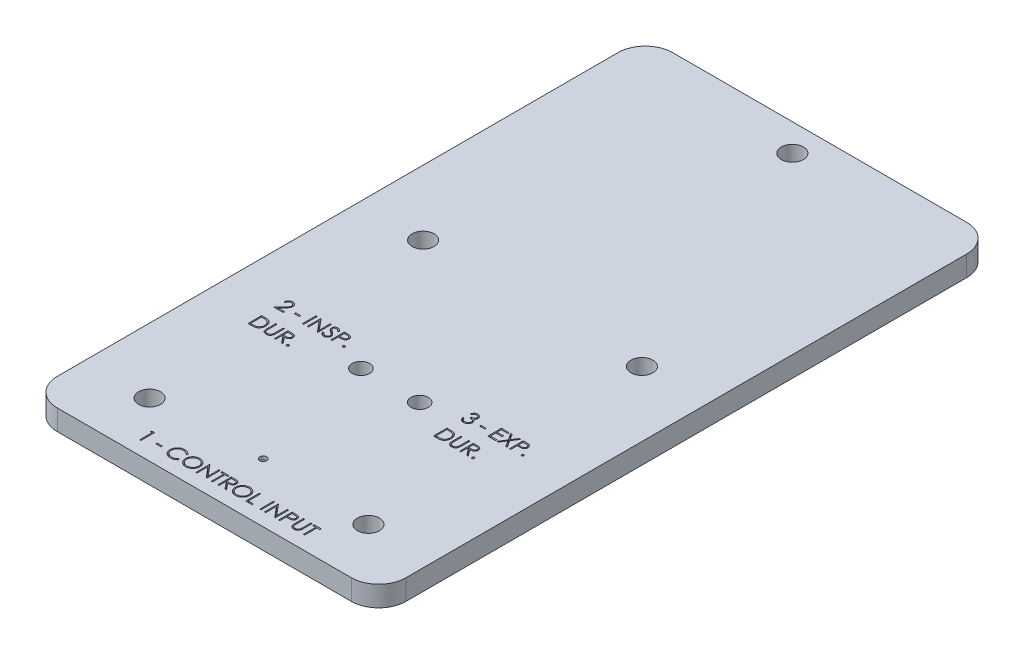
SolidWorks part; units mm, degrees
material "ABS"
ref_plane "Front Plane" through (0, 0, 0) normal (0, 0, 1) x (1, 0, 0)
ref_plane "Top Plane" through (0, 0, 0) normal (0, 1, 0) x (1, 0, 0)
ref_plane "Right Plane" through (0, 0, 0) normal (1, 0, 0) x (0, 0, -1)
sketch "Sketch2" plane through (0, 0, 0) normal (0, 1, 0) x (1, 0, 0)
  line L4 (-40.4812, 114.2369) -> (-40.4812, -15.9381)
  line L5 (-34.1312, -22.2881) -> (34.1313, -22.2881)
  line L6 (40.4813, -15.9381) -> (40.4813, 114.2369)
  line L7 (34.1313, 120.5869) -> (-34.1312, 120.5869)
  line L8 (-40.4812, 114.2369) -> (-40.4812, -15.9381)
  line L9 (-34.1312, -22.2881) -> (34.1313, -22.2881)
  line L10 (40.4813, -15.9381) -> (40.4813, 114.2369)
  line L11 (34.1313, 120.5869) -> (-34.1312, 120.5869)
  circle A0 centre (-25.4, -9.5881) radius 2.5527 construction
  circle A1 centre (25.4, -9.5881) radius 2.5527 construction
  circle A2 centre (25.4, 53.9119) radius 2.5527 construction
  circle A3 centre (0, 114.2369) radius 2.5527 construction
  arc A4 (-40.4812, -15.9381) -> (-34.1312, -22.2881) centre (-34.1312, -15.9381) ccw
  arc A5 (34.1313, -22.2881) -> (40.4813, -15.9381) centre (34.1313, -15.9381) ccw
  arc A6 (40.4813, 114.2369) -> (34.1313, 120.5869) centre (34.1313, 114.2369) ccw
  arc A7 (-34.1312, 120.5869) -> (-40.4812, 114.2369) centre (-34.1312, 114.2369) ccw
  arc A8 (-40.4812, -15.9381) -> (-34.1312, -22.2881) centre (-34.1312, -15.9381) ccw
  arc A9 (34.1313, -22.2881) -> (40.4813, -15.9381) centre (34.1313, -15.9381) ccw
  arc A10 (40.4813, 114.2369) -> (34.1313, 120.5869) centre (34.1313, 114.2369) ccw
  arc A11 (-34.1312, 120.5869) -> (-40.4812, 114.2369) centre (-34.1312, 114.2369) ccw
  circle A12 centre (-25.4, 53.9119) radius 2.5527 construction
  circle A13 centre (-25.4, -9.5881) radius 2.5527
  circle A14 centre (25.4, -9.5881) radius 2.5527
  circle A15 centre (25.4, 53.9119) radius 2.5527
  circle A16 centre (0, 114.2369) radius 2.5527
  circle A17 centre (-25.4, 53.9119) radius 2.5527
  dimension "D1" = 0
extrude "Boss-Extrude1" add sketch "Sketch2" along normal blind 4.7625
hole_wizard "#10-32 Tapped Hole1" positions "Sketch3" profile "Sketch4" tap size "#10-32" standard "ANSI Inch" end condition up to next
sketch "Sketch3" plane through (0, 4.7625, 0) normal (0, 1, 0) x (1, 0, 0)
  point P0 (-6.8202, 20.8982)
  point P3 (6.8202, 20.8982)
sketch "Sketch4" plane through (-6.8202, 4.7625, -20.8982) normal (1, 0, 0) x (0, 0, 1)
  line L0 (0, 0) -> (0, 4.7625)
  line L1 (0, 4.7625) -> (2.0193, 4.7625)
  line L2 (2.0193, 4.7625) -> (2.0193, 0)
  line L5 (2.0193, 0) -> (0, 0)
  line L11 (0, -6.35) -> (0, 107.95) construction
  dimension "Thru Tap Drill Dia." = 4.0386
  dimension "Thru Tap Drill Depth" = 4.7625
cosmetic thread "Hole Thread1" parameters "D2"=4.826
cosmetic thread "Hole Thread2" parameters "D2"=4.826
sketch "Sketch5" plane through (0, 4.7625, 0) normal (0, 1, 0) x (1, 0, 0)
  circle A0 centre (0, -8.5969) radius 0.7937
  dimension "D1" = 1.5875
extrude "Cut-Extrude1" cut sketch "Sketch5" against normal blind 0.762
sketch "Sketch6" plane through (0, 4.7625, 0) normal (0, 1, 0) x (1, 0, 0)
  text T0 "1 - CONTROL INPUT"
  text T1 "2 - INSP.\r\nDUR."
  text T2 "3 - EXP. \r\nDUR."
extrude "Cut-Extrude2" cut sketch "Sketch6" against normal blind 0.7874
